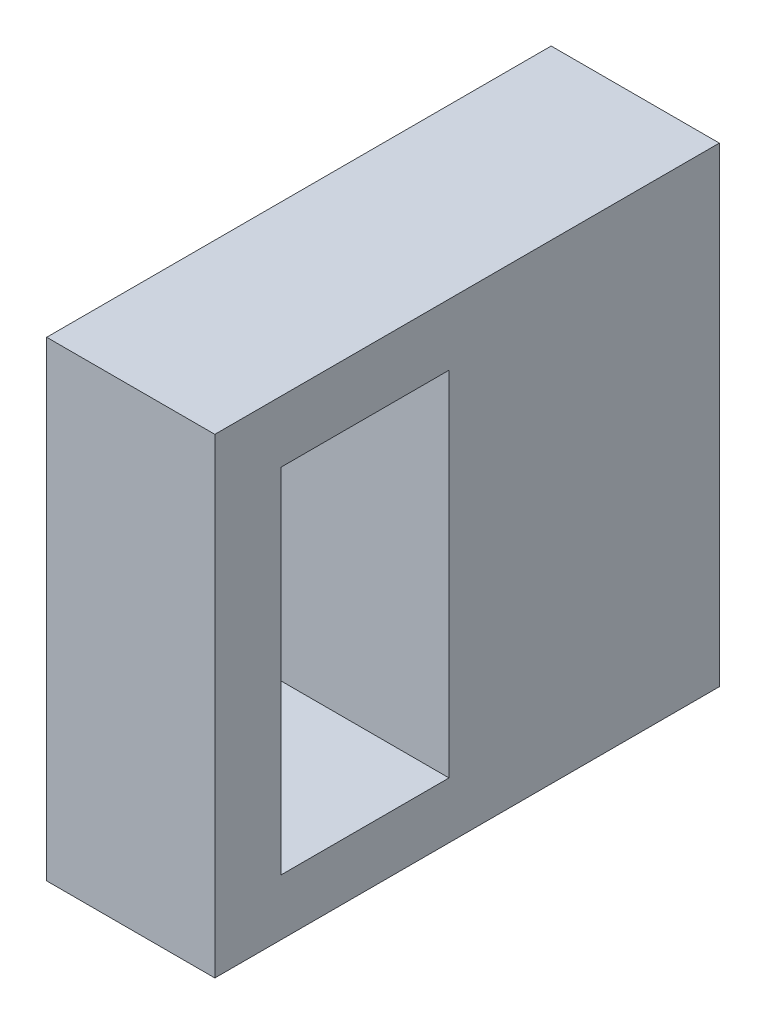
SolidWorks part; units mm, degrees
ref_plane "Alzado" through (0, 0, 0) normal (0, 0, 1) x (1, 0, 0)
ref_plane "Planta" through (0, 0, 0) normal (0, 1, 0) x (1, 0, 0)
ref_plane "Vista lateral" through (0, 0, 0) normal (1, 0, 0) x (0, 0, -1)
sketch "Croquis1" plane through (0, 0, 0) normal (0, 0, 1) x (1, 0, 0)
  line L0 (-43.8459, 37.1175) -> (-31.1459, 37.1175)
  line L1 (-31.1459, 37.1175) -> (-31.1459, 1.5575)
  line L2 (-31.1459, 1.5575) -> (-43.8459, 1.5575)
  line L3 (-43.8459, 1.5575) -> (-43.8459, 37.1175)
extrude "Saliente-Extruir1" add sketch "Croquis1" along normal blind 38.1
sketch "Croquis3" plane through (-43.8459, 0, 0) normal (-1, 0, 0) x (0, 0, 1)
  line L0 (20.4137, 32.4703) -> (20.4137, 5.8003)
  line L1 (20.4137, 5.8003) -> (33.1137, 5.8003)
  line L2 (33.1137, 5.8003) -> (33.1137, 32.4703)
  line L3 (33.1137, 32.4703) -> (20.4137, 32.4703)
  line L4 (38.1, 37.1175) -> (0, 37.1175) construction
  line L5 (38.1, 1.5575) -> (0, 1.5575) construction
  dimension "D1" = 4.6472
  dimension "D2" = 4.2428
  dimension "D3" = 12.7
  dimension "D4" = 26.67
extrude "Cortar-Extruir1" cut sketch "Croquis3" against normal blind 38.1
